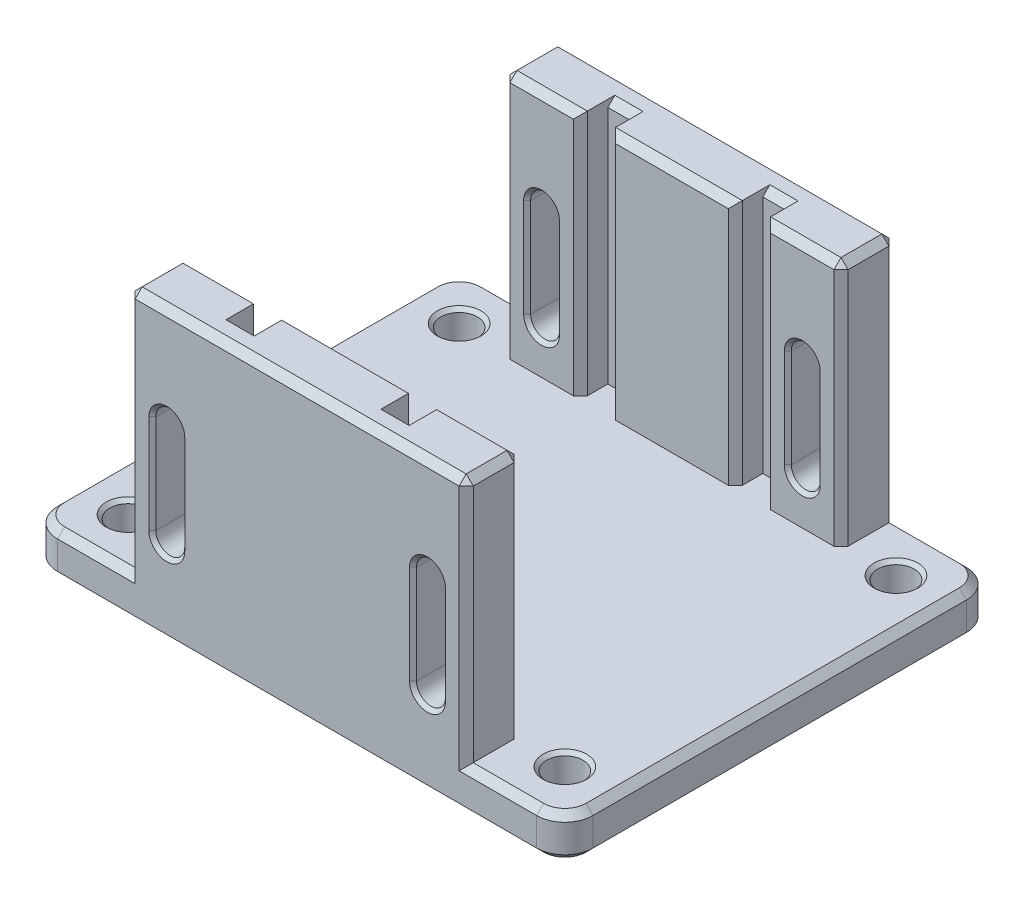
SolidWorks part; units mm, degrees
material "PET"
ref_plane "Front Plane" through (0, 0, 0) normal (0, 0, 1) x (1, 0, 0)
ref_plane "Top Plane" through (0, 0, 0) normal (0, 1, 0) x (1, 0, 0)
ref_plane "Right Plane" through (0, 0, 0) normal (1, 0, 0) x (0, 0, -1)
sketch "Sketch2" plane through (0, 0, 0) normal (1, 0, 0) x (0, 0, -1)
  line L0 (-30.5, 35) -> (-22.7, 35)
  line L1 (-22.7, 35) -> (-22.7, 0)
  line L2 (-22.7, 0) -> (0, 0)
  line L3 (0, 0) -> (22.7, 0)
  line L4 (22.7, 0) -> (22.7, 35)
  line L5 (22.7, 35) -> (30.5, 35)
  line L6 (30.5, 35) -> (30.5, -6)
  line L7 (30.5, -6) -> (-30.5, -6)
  line L8 (-30.5, -6) -> (-30.5, 35)
  dimension "D1" = 45.4
  dimension "D2" = 6
  dimension "D3" = 7.8
  dimension "D4" = 41
extrude "Boss-Extrude1" add sketch "Sketch2" along normal mid plane 48
sketch "Sketch3" plane through (0, 0, 0) normal (0, 0, 1) x (1, 0, 0)
  line L0 (24, 35) -> (-24, 35) construction
  line L1 (-13, 35) -> (-9, 35)
  line L2 (-13, 35) -> (-13, 0)
  line L3 (-13, 0) -> (-9, 0)
  line L4 (-9, 35) -> (-9, 0)
  line L5 (9, 35) -> (13, 35)
  line L6 (9, 35) -> (9, 0)
  line L7 (9, 0) -> (13, 0)
  line L8 (13, 35) -> (13, 0)
  line L9 (24, 0) -> (-24, 0) construction
  line L10 (-13, 35) -> (-24, 35) construction
  line L11 (-24, 35) -> (-24, -6) construction
  line L12 (13, 35) -> (24, 35) construction
  line L13 (24, 35) -> (24, 0) construction
  dimension "D1" = 11
  dimension "D2" = 4
extrude "Cut-Extrude1" cut sketch "Sketch3" against normal mid plane 53.2
sketch "Sketch4" plane through (0, 0, 0) normal (0, 0, 1) x (1, 0, 0)
  line L0 (-18.5, 20.5) -> (-18.5, 6.5) construction
  line L1 (-16.45, 20.5) -> (-16.45, 6.5)
  line L2 (-20.55, 20.5) -> (-20.55, 6.5)
  line L3 (-18.5, 13.5) -> (-24, 13.5) construction
  line L4 (18.5, 13.5) -> (24, 13.5) construction
  line L5 (18.5, 20.5) -> (18.5, 6.5) construction
  line L6 (20.55, 20.5) -> (20.55, 6.5)
  line L7 (16.45, 20.5) -> (16.45, 6.5)
  line L8 (-24, 35) -> (-24, -6) construction
  line L9 (-18.5, 20.5) -> (-18.5, 26) construction
  line L10 (-18.5, 26) -> (-18.5, 35) construction
  line L11 (-18.5, 6.5) -> (-18.5, 1) construction
  line L13 (24, 35) -> (24, -6) construction
  line L14 (24, 35) -> (-24, 35) construction
  line L15 (-18.5, 1) -> (-18.5, 0) construction
  line L16 (-13, 0) -> (-24, 0) construction
  arc A0 (-16.45, 20.5) -> (-20.55, 20.5) centre (-18.5, 20.5) ccw
  arc A1 (-20.55, 6.5) -> (-16.45, 6.5) centre (-18.5, 6.5) ccw
  arc A2 (20.55, 20.5) -> (16.45, 20.5) centre (18.5, 20.5) ccw
  arc A3 (16.45, 6.5) -> (20.55, 6.5) centre (18.5, 6.5) ccw
  point P2 (-18.5, 13.5)
  point P9 (18.5, 13.5)
  dimension "D1" = 4.1
  dimension "D2" = 5.5
  dimension "D3" = 9
  dimension "D4" = 1
extrude "Cut-Extrude2" cut sketch "Sketch4" against normal through all both and the other way through all
sketch "Sketch5" plane through (0, 0, 0) normal (0, 1, 0) x (1, 0, 0)
  line L0 (-20.55, -30.5) -> (-16.45, -30.5) construction
  line L1 (-24, 30.5) -> (-38, 30.5)
  line L2 (-24, 30.5) -> (-24, -30.5)
  line L3 (-24, -30.5) -> (-38, -30.5)
  line L4 (-38, 30.5) -> (-38, -30.5)
  line L5 (24, 30.5) -> (38, 30.5)
  line L6 (24, 30.5) -> (24, -30.5)
  line L7 (24, -30.5) -> (38, -30.5)
  line L8 (38, 30.5) -> (38, -30.5)
  line L9 (-16.45, 30.5) -> (-20.55, 30.5) construction
  line L10 (-24, -22.7) -> (-24, -30.5) construction
  line L11 (24, -30.5) -> (24, 30.5) construction
  line L12 (-38, 30.5) -> (-24, 16.5) construction
  line L13 (-31, 30.5) -> (-31, 23.5) construction
  line L14 (-24, 22.7) -> (-24, -22.7) construction
  line L15 (-31, 23.5) -> (-24, 23.5) construction
  line L16 (24, 30.5) -> (38, 16.5) construction
  line L17 (-24, 23.5) -> (31, 23.5) construction
  line L18 (-38, -16.5) -> (-24, -30.5) construction
  line L19 (24, -16.5) -> (38, -30.5) construction
  line L20 (-31, -23.5) -> (-31, -30.5) construction
  line L21 (-31, -23.5) -> (-38, -23.5) construction
  line L22 (-31, -23.5) -> (31, -23.5) construction
  circle A0 centre (-31, 23.5) radius 2.6
  circle A1 centre (31, 23.5) radius 2.6
  circle A2 centre (-31, -23.5) radius 2.6
  circle A3 centre (31, -23.5) radius 2.6
  dimension "D2" = 5.2
  dimension "D1" = 14
extrude "Boss-Extrude2" add sketch "Sketch5" against normal up to surface (6 mm away) up to face at (0, -6, 0)
fillet "Fillet1" radius 4 4 edges at (-38, -3, -30.5) (-38, -3, 30.5) (38, -3, -30.5) (38, -3, 30.5)
chamfer "Chamfer1" distance 1 angle 45 50 edges at (0, -6, 30.5) (-38, 0, 0) (-38, -6, 0) (0, -6, -30.5) (38, -6, 0) (38, 0, 0) (0, 35, -22.7) (18.5, 35, -22.7) (24, 35, -26.6) (0, 35, -30.5) (-24, 35, -26.6) (-18.5, 35, -22.7) (0, 35, 22.7) (-18.5, 35, 22.7) (-24, 35, 26.6) (0, 35, 30.5) (18.5, 35, 22.7) (24, 35, 26.6) (-11, 35, -26.6) (11, 35, -26.6) (-11, 35, 26.6) (11, 35, 26.6) (-29, 0, 30.5) (-29, 0, -30.5) (29, 0, 30.5) (29, 0, -30.5) (24, 17.5, 30.5) (24, 17.5, -30.5) (9, 17.5, -22.7) (-9, 17.5, -22.7) (9, 17.5, 22.7) (-9, 17.5, 22.7) (24, 17.5, 22.7) (13, 17.5, 22.7) (-13, 17.5, 22.7) (24, 17.5, -22.7) (13, 17.5, -22.7) (-13, 17.5, -22.7) (-24, 17.5, 30.5) (-24, 17.5, -22.7) (-24, 17.5, -30.5) (-24, 17.5, 22.7) (-36.8284, -6, 29.3284) (36.8284, -6, 29.3284) (36.8284, -6, -29.3284) (-36.8284, -6, -29.3284) (36.8284, 0, -29.3284) (-36.8284, 0, -29.3284) (36.8284, 0, 29.3284) (-36.8284, 0, 29.3284)
chamfer "Chamfer2" distance 0.5 angle 45 40 edges at (20.55, 13.5, -30.5) (18.5, 22.55, -30.5) (18.5, 4.45, -30.5) (16.45, 13.5, -30.5) (20.55, 13.5, -22.7) (18.5, 4.45, -22.7) (18.5, 22.55, -22.7) (16.45, 13.5, -22.7) (-16.45, 13.5, -30.5) (-18.5, 22.55, -30.5) (-18.5, 4.45, -30.5) (-20.55, 13.5, -30.5) (-16.45, 13.5, -22.7) (-18.5, 4.45, -22.7) (-18.5, 22.55, -22.7) (-20.55, 13.5, -22.7) (-16.45, 13.5, 22.7) (-18.5, 22.55, 22.7) (-18.5, 4.45, 22.7) (-20.55, 13.5, 22.7) (20.55, 13.5, 22.7) (18.5, 22.55, 22.7) (18.5, 4.45, 22.7) (16.45, 13.5, 22.7) (-16.45, 13.5, 30.5) (-18.5, 22.55, 30.5) (-18.5, 4.45, 30.5) (-20.55, 13.5, 30.5) (20.55, 13.5, 30.5) (18.5, 22.55, 30.5) (18.5, 4.45, 30.5) (16.45, 13.5, 30.5) (-31, -6, -20.9) (-31, -6, 26.1) (31, -6, 26.1) (31, -6, -20.9) (-31, 0, -20.9) (-31, 0, 26.1) (31, 0, -20.9) (31, 0, 26.1)
